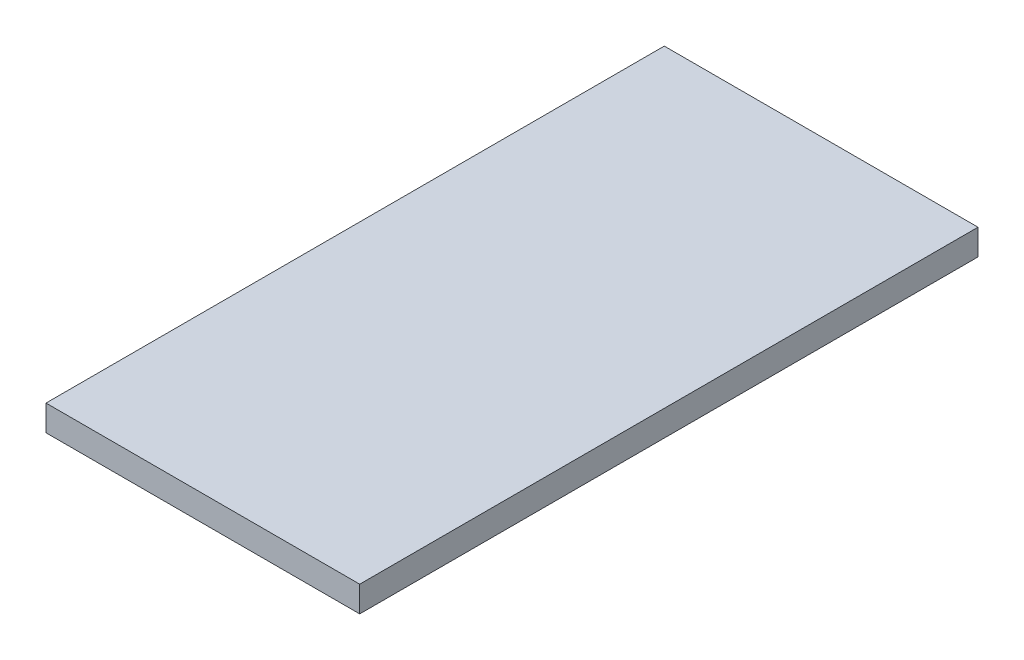
SolidWorks part; units mm, degrees
ref_plane "Front Plane" through (0, 0, 0) normal (0, 0, 1) x (1, 0, 0)
ref_plane "Top Plane" through (0, 0, 0) normal (0, 1, 0) x (1, 0, 0)
ref_plane "Right Plane" through (0, 0, 0) normal (1, 0, 0) x (0, 0, -1)
sketch "Sketch1" plane through (0, 0, 0) normal (0, 0, 1) x (1, 0, 0)
  line L0 (-105, 12.7) -> (-105, 0) construction
  line L1 (86.8758, 57.4) -> (-67.7742, 57.4)
  line L2 (86.8758, 57.4) -> (86.8758, 44.7)
  line L3 (86.8758, 44.7) -> (-67.7742, 44.7)
  line L4 (-67.7742, 57.4) -> (-67.7742, 44.7)
  line L5 (-67.7742, 17.1) -> (-67.7742, 8.3) construction
  line L6 (86.8758, 96.0833) -> (86.8758, 66.2167) construction
  line L7 (-75.5, 44.7) -> (-102.5, 44.7) construction
extrude "Boss-Extrude1" add sketch "Sketch1" against normal blind 304.8 contours L1 L4 L3 L2
sketch "Sketch2"
  line L1 (-86.8758, 304.8) -> (-86.8758, 0) construction
  line L2 (-86.8758, 0) -> (67.7742, 0) construction
  line L3 (-86.8758, 304.8) -> (67.7742, 304.8) construction
  line L4 (67.7742, 304.8) -> (67.7742, 0) construction
  point P0 (-70.8758, 72.87)
  point P1 (-30.8758, 64.87)
  point P2 (-70.8758, 56.87)
  point P3 (-38.8758, 72.87)
  point P4 (-38.8758, 56.87)
  point P5 (-78.8758, 64.87)
  point P6 (-70.8758, 223.85)
  point P7 (-30.8758, 215.85)
  point P8 (-70.8758, 207.85)
  point P9 (-38.8758, 223.85)
  point P10 (-38.8758, 207.85)
  point P11 (-78.8758, 215.85)
  point P12 (61.4242, 298.45)
  point P13 (61.4242, 6.35)
  point P14 (0, 0)
other "AlignGroup1" parameters "D1"=9.4322, "D2"=8, "D3"=16, "D4"=48, "D5"=56, "D6"=24.5862, "D7"=33.9802, "D8"=16, "D9"=8, "D10"=0, "D11"=16, "D12"=8, "D13"=0, "D14"=8, "D15"=40, "D16"=48, "D17"=53.1226, "D18"=124.0061, "D19"=304.8, "D20"=13.3035, "D21"=18.3355
other "AlignGroup2"
other "AlignGroup3"
other "AlignGroup4"
